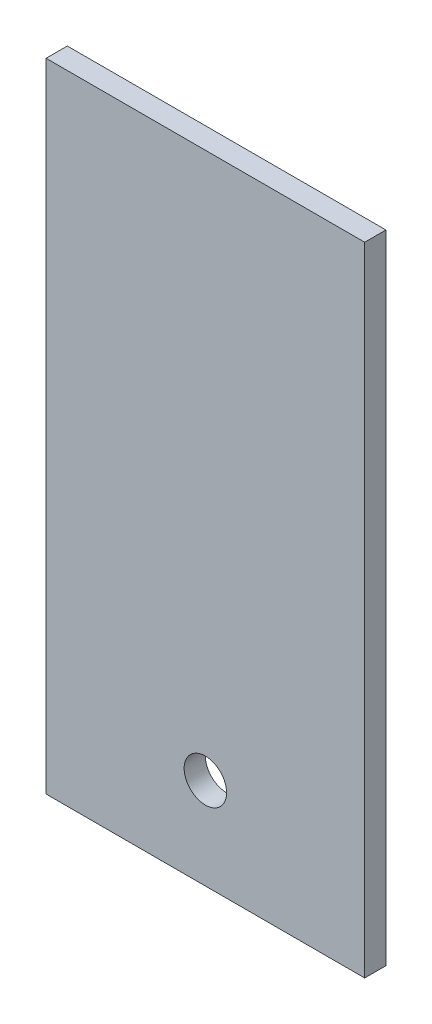
SolidWorks part; units mm, degrees
ref_plane "Front Plane" through (0, 0, 0) normal (0, 0, 1) x (1, 0, 0)
ref_plane "Top Plane" through (0, 0, 0) normal (0, 1, 0) x (1, 0, 0)
ref_plane "Right Plane" through (0, 0, 0) normal (1, 0, 0) x (0, 0, -1)
sketch "Sketch1" plane through (0, 0, 0) normal (0, 0, 1) x (1, 0, 0)
  line L1 (-75, 150) -> (75, 150)
  line L2 (-75, 150) -> (-75, -150)
  line L3 (-75, -150) -> (75, -150)
  line L4 (75, 150) -> (75, -150)
  line L5 (-75, 150) -> (75, -150) construction
  line L6 (-75, -150) -> (75, 150) construction
  circle A0 centre (0, -107) radius 10
  point P0 (0, 0)
  dimension "D4" = 20
  dimension "D1" = 150
  dimension "D2" = 300
  dimension "D3" = 257
extrude "Boss-Extrude1" add sketch "Sketch1" along normal blind 10
